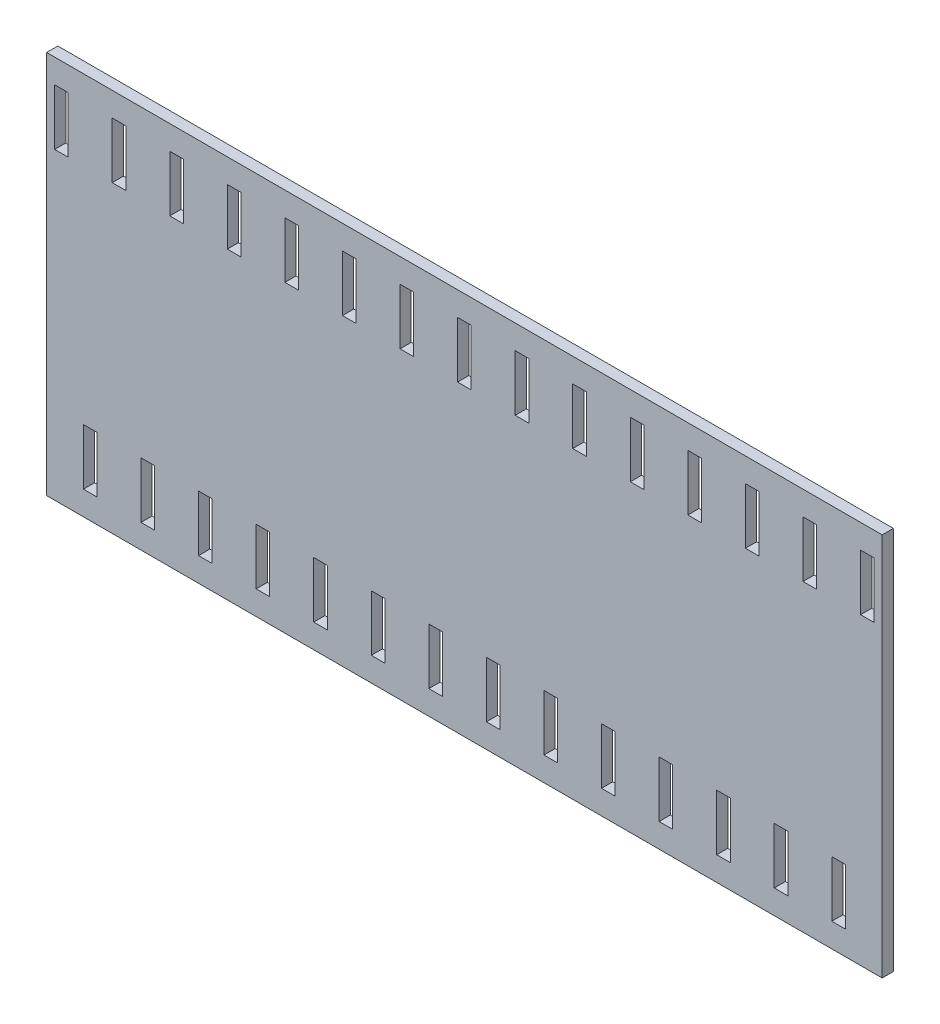
SolidWorks part; units mm, degrees
ref_plane "Plan de face" through (0, 0, 0) normal (0, 0, 1) x (1, 0, 0)
ref_plane "Plan de dessus" through (0, 0, 0) normal (0, 1, 0) x (1, 0, 0)
ref_plane "Plan de droite" through (0, 0, 0) normal (1, 0, 0) x (0, 0, -1)
sketch "Esquisse1" plane through (0, 0, 0) normal (0, 0, 1) x (1, 0, 0)
  line L1 (-52.25, -24) -> (52.25, -24)
  line L2 (-52.25, -24) -> (-52.25, 24)
  line L3 (-52.25, 24) -> (52.25, 24)
  line L4 (52.25, -24) -> (52.25, 24)
  line L5 (-52.25, -24) -> (52.25, 24) construction
  line L6 (-52.25, 24) -> (52.25, -24) construction
  point P0 (0, 0)
  dimension "D1" = 104.5
  dimension "D2" = 48
extrude "Boss.-Extru.1" add sketch "Esquisse1" along normal blind 1.4
sketch "Esquisse2" plane through (0, 0, 0) normal (0, 0, -1) x (-1, 0, 0)
  line L0 (-52.25, 24) -> (52.25, 24) construction
  line L1 (-51.25, 21) -> (-49.55, 21)
  line L2 (-51.25, 21) -> (-51.25, 14)
  line L3 (-51.25, 14) -> (-49.55, 14)
  line L4 (-49.55, 21) -> (-49.55, 14)
  line L5 (-52.25, -24) -> (-52.25, 24) construction
  line L6 (-44.05, 21) -> (-44.05, 14)
  line L7 (-44.05, 21) -> (-42.35, 21)
  line L8 (-42.35, 21) -> (-42.35, 14)
  line L9 (-44.05, 14) -> (-42.35, 14)
  line L10 (-36.85, 21) -> (-36.85, 14)
  line L11 (-36.85, 21) -> (-35.15, 21)
  line L12 (-35.15, 21) -> (-35.15, 14)
  line L13 (-36.85, 14) -> (-35.15, 14)
  line L14 (-29.65, 21) -> (-29.65, 14)
  line L15 (-29.65, 21) -> (-27.95, 21)
  line L16 (-27.95, 21) -> (-27.95, 14)
  line L17 (-29.65, 14) -> (-27.95, 14)
  line L18 (-22.45, 21) -> (-22.45, 14)
  line L19 (-22.45, 21) -> (-20.75, 21)
  line L20 (-20.75, 21) -> (-20.75, 14)
  line L21 (-22.45, 14) -> (-20.75, 14)
  line L22 (-15.25, 21) -> (-15.25, 14)
  line L23 (-15.25, 21) -> (-13.55, 21)
  line L24 (-13.55, 21) -> (-13.55, 14)
  line L25 (-15.25, 14) -> (-13.55, 14)
  line L26 (-8.05, 21) -> (-8.05, 14)
  line L27 (-8.05, 21) -> (-6.35, 21)
  line L28 (-6.35, 21) -> (-6.35, 14)
  line L29 (-8.05, 14) -> (-6.35, 14)
  line L30 (-0.85, 21) -> (-0.85, 14)
  line L31 (-0.85, 21) -> (0.85, 21)
  line L32 (0.85, 21) -> (0.85, 14)
  line L33 (-0.85, 14) -> (0.85, 14)
  line L34 (6.35, 21) -> (6.35, 14)
  line L35 (6.35, 21) -> (8.05, 21)
  line L36 (8.05, 21) -> (8.05, 14)
  line L37 (6.35, 14) -> (8.05, 14)
  line L38 (13.55, 21) -> (13.55, 14)
  line L39 (13.55, 21) -> (15.25, 21)
  line L40 (15.25, 21) -> (15.25, 14)
  line L41 (13.55, 14) -> (15.25, 14)
  line L42 (20.75, 21) -> (20.75, 14)
  line L43 (20.75, 21) -> (22.45, 21)
  line L44 (22.45, 21) -> (22.45, 14)
  line L45 (20.75, 14) -> (22.45, 14)
  line L46 (27.95, 21) -> (27.95, 14)
  line L47 (27.95, 21) -> (29.65, 21)
  line L48 (29.65, 21) -> (29.65, 14)
  line L49 (27.95, 14) -> (29.65, 14)
  line L50 (35.15, 21) -> (35.15, 14)
  line L51 (35.15, 21) -> (36.85, 21)
  line L52 (36.85, 21) -> (36.85, 14)
  line L53 (35.15, 14) -> (36.85, 14)
  line L54 (42.35, 21) -> (42.35, 14)
  line L55 (42.35, 21) -> (44.05, 21)
  line L56 (44.05, 21) -> (44.05, 14)
  line L57 (42.35, 14) -> (44.05, 14)
  line L58 (49.55, 21) -> (49.55, 14)
  line L59 (49.55, 21) -> (51.25, 21)
  line L60 (51.25, 21) -> (51.25, 14)
  line L61 (49.55, 14) -> (51.25, 14)
  line L62 (52.25, -24) -> (-52.25, -24) construction
  line L63 (-47.65, -14) -> (-45.95, -14)
  line L64 (-47.65, -14) -> (-47.65, -21)
  line L65 (-47.65, -21) -> (-45.95, -21)
  line L66 (-45.95, -14) -> (-45.95, -21)
  line L67 (-40.45, -14) -> (-40.45, -21)
  line L68 (-40.45, -14) -> (-38.75, -14)
  line L69 (-38.75, -14) -> (-38.75, -21)
  line L70 (-40.45, -21) -> (-38.75, -21)
  line L71 (-33.25, -14) -> (-33.25, -21)
  line L72 (-33.25, -14) -> (-31.55, -14)
  line L73 (-31.55, -14) -> (-31.55, -21)
  line L74 (-33.25, -21) -> (-31.55, -21)
  line L75 (-26.05, -14) -> (-26.05, -21)
  line L76 (-26.05, -14) -> (-24.35, -14)
  line L77 (-24.35, -14) -> (-24.35, -21)
  line L78 (-26.05, -21) -> (-24.35, -21)
  line L79 (-18.85, -14) -> (-18.85, -21)
  line L80 (-18.85, -14) -> (-17.15, -14)
  line L81 (-17.15, -14) -> (-17.15, -21)
  line L82 (-18.85, -21) -> (-17.15, -21)
  line L83 (-11.65, -14) -> (-11.65, -21)
  line L84 (-11.65, -14) -> (-9.95, -14)
  line L85 (-9.95, -14) -> (-9.95, -21)
  line L86 (-11.65, -21) -> (-9.95, -21)
  line L87 (-4.45, -14) -> (-4.45, -21)
  line L88 (-4.45, -14) -> (-2.75, -14)
  line L89 (-2.75, -14) -> (-2.75, -21)
  line L90 (-4.45, -21) -> (-2.75, -21)
  line L91 (2.75, -14) -> (2.75, -21)
  line L92 (2.75, -14) -> (4.45, -14)
  line L93 (4.45, -14) -> (4.45, -21)
  line L94 (2.75, -21) -> (4.45, -21)
  line L95 (9.95, -14) -> (9.95, -21)
  line L96 (9.95, -14) -> (11.65, -14)
  line L97 (11.65, -14) -> (11.65, -21)
  line L98 (9.95, -21) -> (11.65, -21)
  line L99 (17.15, -14) -> (17.15, -21)
  line L100 (17.15, -14) -> (18.85, -14)
  line L101 (18.85, -14) -> (18.85, -21)
  line L102 (17.15, -21) -> (18.85, -21)
  line L103 (24.35, -14) -> (24.35, -21)
  line L104 (24.35, -14) -> (26.05, -14)
  line L105 (26.05, -14) -> (26.05, -21)
  line L106 (24.35, -21) -> (26.05, -21)
  line L107 (31.55, -14) -> (31.55, -21)
  line L108 (31.55, -14) -> (33.25, -14)
  line L109 (33.25, -14) -> (33.25, -21)
  line L110 (31.55, -21) -> (33.25, -21)
  line L111 (38.75, -14) -> (38.75, -21)
  line L112 (38.75, -14) -> (40.45, -14)
  line L113 (40.45, -14) -> (40.45, -21)
  line L114 (38.75, -21) -> (40.45, -21)
  line L115 (45.95, -14) -> (45.95, -21)
  line L116 (45.95, -14) -> (47.65, -14)
  line L117 (47.65, -14) -> (47.65, -21)
  line L118 (45.95, -21) -> (47.65, -21)
  dimension "D1" = 1.7
  dimension "D2" = 7
  dimension "D3" = 3
  dimension "D4" = 1
  dimension "D6" = 1.7
  dimension "D7" = 4.6
  dimension "D8" = 3
  dimension "D9" = 7
  dimension "D5" = 15
  dimension "D10" = 14
extrude "Enlèv. mat.-Extru.1" cut sketch "Esquisse2" against normal through all
sketch "Esquisse4" plane through (0, 0, 0) normal (0, 0, -1) x (-1, 0, 0)
  text T0 "PCB - PAPER"
extrude "Enlèv. mat.-Extru.2" cut sketch "Esquisse4" against normal blind 0.1
